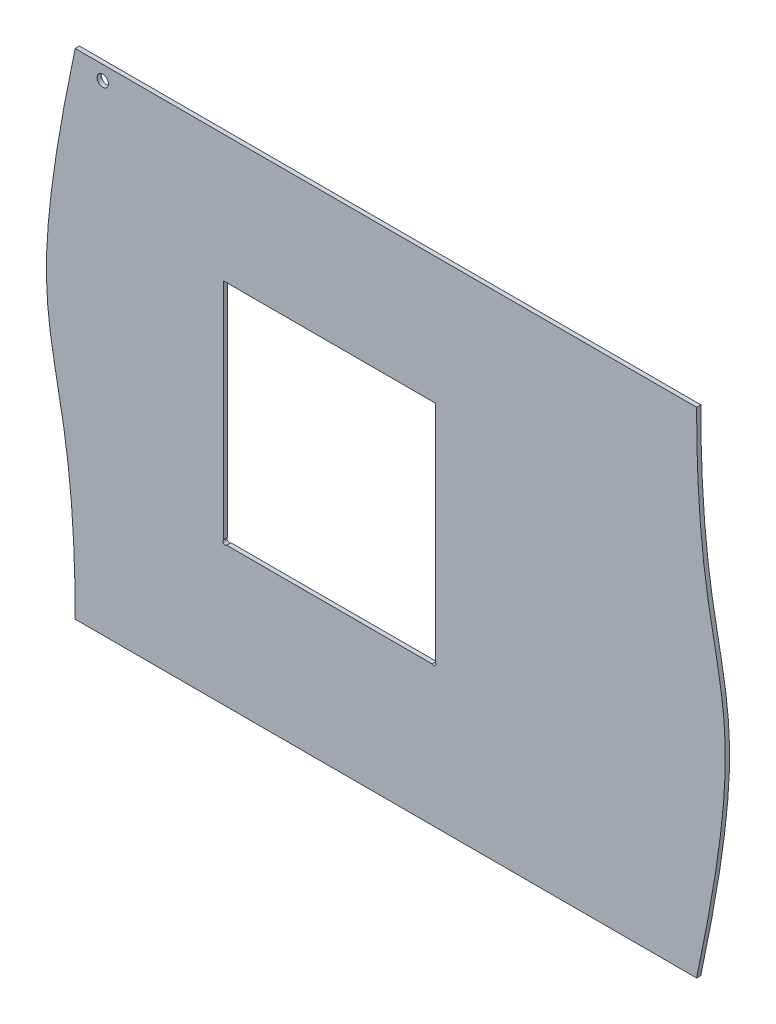
SolidWorks part; units mm, degrees
ref_plane "Plan de face" through (0, 0, 0) normal (0, 0, 1) x (1, 0, 0)
ref_plane "Plan de dessus" through (0, 0, 0) normal (0, 1, 0) x (1, 0, 0)
ref_plane "Plan de droite" through (0, 0, 0) normal (1, 0, 0) x (0, 0, -1)
sketch "Esquisse1" plane through (0, 0, 0) normal (0, 0, 1) x (1, 0, 0)
  line L0 (536.5085, 0) -> (-13.3743, 0) construction
  line L1 (-10, 8) -> (430, 8)
  line L3 (-10, 358) -> (430, 358)
  line L5 (0, 317.0008) -> (0, 420.4252) construction
  line L6 (420, -67.8064) -> (420, 420.4252) construction
  line L7 (-58.7504, 358) -> (536.5085, 358) construction
  line L8 (-44.4443, 8) -> (504.1642, 8) construction
  line L9 (-58.7504, 183) -> (504.1642, 183) construction
  line L10 (210, -34.4525) -> (210, 403.8703) construction
  line L11 (95, 312.8184) -> (95, 62.6795) construction
  line L12 (245, 312.8184) -> (245, 77.601) construction
  line L13 (44.0199, 268) -> (294.4824, 268) construction
  line L14 (95, 268) -> (95, 109.2627)
  line L15 (170, 297.7251) -> (170, 173.0003) construction
  line L35 (245, 268) -> (95, 268)
  line L39 (245, 109.2627) -> (245, 268)
  line L42 (37.67, 107) -> (257.0223, 107) construction
  line L43 (97.2627, 107) -> (242.7373, 107)
  line L59 (-30, -67.8064) -> (-30, 412.0672) construction
  line L60 (-10, 374.1921) -> (-10, -22.9336) construction
  line L61 (-20, 196.1893) -> (-20, 121.5026) construction
  line L63 (-44.4443, 158) -> (15.8377, 158) construction
  line L64 (-58.7504, 208) -> (12.2974, 208) construction
  line L80 (430, 429.0413) -> (430, 142.9931) construction
  line L84 (95, 107) -> (145.4679, 157.4679) construction
  line L90 (-13.3743, 348) -> (53.3664, 348) construction
  line L92 (9.5, 333.4562) -> (9.5, 351.4952) construction
  arc A26 (95, 109.2627) -> (97.2627, 107) centre (96.1314, 108.1314) ccw
  arc A29 (245, 109.2627) -> (242.7373, 107) centre (243.8686, 108.1314) cw
  circle A34 centre (9.5, 348) radius 4
  spline S0 degree 3 poles (-10, 358) (-55.762, 141.1251) (-10, 195.4586) (-10, 8) knots 0 0 0 0 1 1 1 1
  spline S2 degree 3 poles (430, 8) (475.762, 224.8749) (430, 170.5414) (430, 358) knots 0 0 0 0 1 1 1 1
  dimension "D30" = 30
  dimension "D48" = 10
  dimension "D52" = 45
  dimension "D1" = 8
  dimension "D2" = 358
  dimension "D4" = 150
  dimension "D5" = 420
  dimension "D7" = 175
  dimension "D8" = 175
  dimension "D9" = 90
  dimension "D10" = 75
  dimension "D28" = 210
  dimension "D31" = 20
  dimension "D32" = 10
  dimension "D33" = 150
  dimension "D34" = 150
  dimension "D51" = 9.5
extrude "Boss.-Extru.1" add sketch "Esquisse1" along normal blind 3
